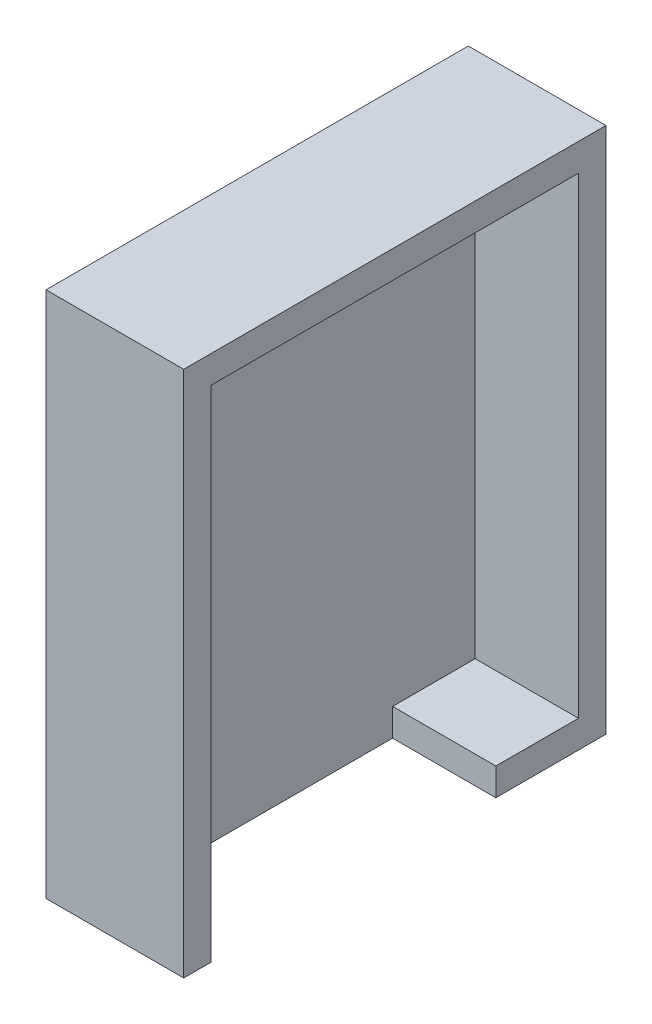
SolidWorks part; units mm, degrees
material "ABS"
ref_plane "Front Plane" through (0, 0, 0) normal (0, 0, 1) x (1, 0, 0)
ref_plane "Top Plane" through (0, 0, 0) normal (0, 1, 0) x (1, 0, 0)
ref_plane "Right Plane" through (0, 0, 0) normal (1, 0, 0) x (0, 0, -1)
sketch "Sketch1" plane through (0, 0, 0) normal (1, 0, 0) x (0, 0, -1)
  line L0 (-4, 4) -> (-4, -72.58)
  line L1 (0, 0) -> (53.34, 0)
  line L2 (0, 0) -> (0, -68.58)
  line L3 (0, -68.58) -> (53.34, -68.58)
  line L4 (53.34, 0) -> (53.34, -68.58)
  line L5 (-4, -72.58) -> (57.34, -72.58)
  line L6 (57.34, 4) -> (57.34, -72.58)
  line L7 (-4, 4) -> (57.34, 4)
  dimension "D1" = 53.34
  dimension "D2" = 68.58
  dimension "D3" = 4
extrude "Boss-Extrude1" add sketch "Sketch1" along normal blind 15
sketch "Sketch2" plane through (0, 0, 0) normal (-1, 0, 0) x (0, 0, 1)
  line L1 (-57.34, 4) -> (4, 4)
  line L2 (-57.34, 4) -> (-57.34, -72.58)
  line L3 (-57.34, -72.58) -> (4, -72.58)
  line L4 (4, 4) -> (4, -72.58)
extrude "Boss-Extrude2" add sketch "Sketch2" along normal blind 5
sketch "Sketch4" plane through (0, -72.58, 0) normal (0, -1, 0) x (-1, 0, 0)
  line L1 (-19.05, 0) -> (0, 0)
  line L2 (-19.05, 0) -> (-19.05, 53.34)
  line L3 (-19.05, 53.34) -> (0, 53.34)
  line L4 (0, 0) -> (0, 53.34)
  line L5 (-15, -4) -> (5, -4) construction
  line L6 (-15, 57.34) -> (5, 57.34) construction
  line L7 (5, 57.34) -> (5, -4) construction
  dimension "D1" = 4
  dimension "D2" = 4
  dimension "D3" = 19.05
  dimension "D4" = 5
extrude "Cut-Extrude2" cut sketch "Sketch4" against normal blind 21
sketch "Sketch5" plane through (0, 0, 0) normal (1, 0, 0) x (0, 0, -1)
  line L0 (0, -72.58) -> (53.34, -72.58) construction
  line L1 (41.34, -72.58) -> (53.34, -72.58)
  line L2 (41.34, -72.58) -> (41.34, -68.58)
  line L3 (41.34, -68.58) -> (53.34, -68.58)
  line L4 (53.34, -72.58) -> (53.34, -68.58)
  line L5 (53.34, -72.58) -> (53.34, 0) construction
  dimension "D1" = 4
  dimension "D2" = 12
extrude "Boss-Extrude3" add sketch "Sketch5" along normal up to surface (15 mm away) up to face at (15, -35.29, -26.67)
